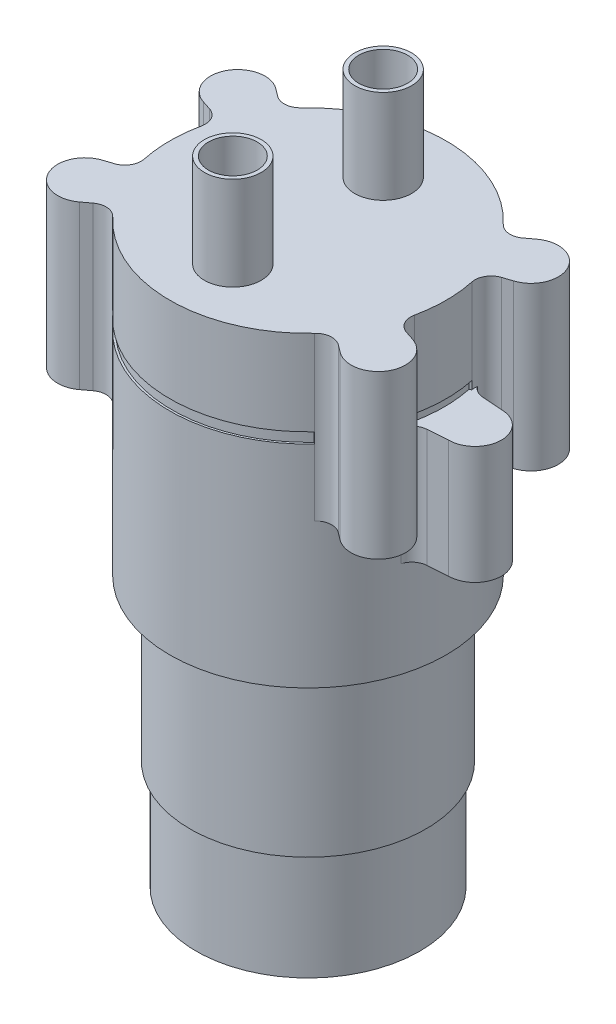
SolidWorks part; units mm, degrees
ref_plane "Plano frontal" through (0, 0, 0) normal (0, 0, 1) x (1, 0, 0)
ref_plane "Plano superior" through (0, 0, 0) normal (0, 1, 0) x (1, 0, 0)
ref_plane "Plano direito" through (0, 0, 0) normal (1, 0, 0) x (0, 0, -1)
sketch "Esboço1" plane through (0, 0, 0) normal (0, 0, 1) x (1, 0, 0)
  line L0 (0, 52.0087) -> (0, -22.4913)
  line L1 (0, 52.0087) -> (17, 52.0087)
  line L2 (17, 52.0087) -> (17, 41.5087)
  line L3 (17, 41.5087) -> (16.75, 41.5087)
  line L4 (16.75, 41.5087) -> (16.75, 40.2087)
  line L5 (16.75, 40.2087) -> (17, 40.2087)
  line L6 (17, 40.2087) -> (17, 14.2087)
  line L7 (17, 14.2087) -> (14.5, 14.2087)
  line L8 (14.5, 14.2087) -> (14.5, -5.5913)
  line L9 (14.5, -5.5913) -> (13.75, -5.5913)
  line L10 (13.75, -5.5913) -> (13.75, -18.9913)
  line L11 (13.75, -18.9913) -> (5, -18.9913)
  line L12 (5, -18.9913) -> (5, -21.4913)
  line L13 (5, -21.4913) -> (1.15, -21.4913)
  line L14 (1.15, -21.4913) -> (1.15, -22.4913)
  line L15 (1.15, -22.4913) -> (0, -22.4913)
  dimension "D1" = 1.15
  dimension "D2" = 5
  dimension "D3" = 13.75
  dimension "D4" = 14.5
  dimension "D5" = 26
  dimension "D6" = 16.75
  dimension "D7" = 1.3
  dimension "D8" = 10.5
  dimension "D9" = 19.8
  dimension "D10" = 13.4
  dimension "D11" = 2.5
  dimension "D12" = 1
revolve "Revolução1" add sketch "Esboço1" angle 360 about L0
sketch "Esboço2" plane through (0, 52.0087, 0) normal (0, 1, 0) x (1, 0, 0)
  line L0 (0, 0) -> (4.923, 2.5639) construction
  line L2 (-10.175, 0) -> (-9.846, 0) construction
  line L3 (18.0489, 9.4) -> (10.175, 0) construction
  line L4 (18.0489, -9.4) -> (10.175, 0) construction
  line L5 (18.0489, 12.75) -> (18.0489, 5.8769) construction
  line L6 (15.0926, 11.3673) -> (16.0335, 12.0759)
  line L7 (17.966, 5.8499) -> (19.0861, 6.2146)
  line L8 (15.0926, -11.3673) -> (16.0335, -12.0759)
  line L9 (17.966, -5.8499) -> (19.0861, -6.2146)
  line L10 (0, 21.7724) -> (0, 5.1279) construction
  line L11 (-18.0489, 12.75) -> (-18.0489, 5.8769) construction
  line L12 (-18.0489, -9.4) -> (-10.175, 0) construction
  line L13 (-18.0489, 9.4) -> (-10.175, 0) construction
  line L14 (0, 0) -> (-4.923, -2.5639) construction
  line L15 (0, 0) -> (-4.923, 2.5639) construction
  line L16 (-17.966, -5.8499) -> (-19.0861, -6.2146)
  line L17 (-15.0926, -11.3673) -> (-16.0335, -12.0759)
  line L18 (-17.966, 5.8499) -> (-19.0861, 6.2146)
  line L19 (-15.0926, 11.3673) -> (-16.0335, 12.0759)
  line L20 (18.0489, -5.8769) -> (18.0489, -12.75) construction
  line L21 (-18.0489, -5.8769) -> (-18.0489, -12.75) construction
  line L22 (12.4273, -11.6001) -> (0, -5.1279)
  line L23 (-12.4273, 11.6001) -> (0, 5.1279)
  line L24 (16.6289, 3.5326) -> (9.846, 0)
  line L25 (12.4273, 11.6001) -> (0, 5.1279)
  line L26 (0, -5.1279) -> (-12.4273, -11.6001)
  line L27 (0, -5.1279) -> (0, -25.7461) construction
  line L28 (-9.846, 0) -> (-16.6289, 3.5326)
  line L29 (9.846, 0) -> (10.175, 0) construction
  line L30 (-9.846, 0) -> (-16.6289, -3.5326)
  line L31 (9.846, 0) -> (16.6289, -3.5326)
  arc A0 (19.0861, 6.2146) -> (16.0335, 12.0759) centre (18.0489, 9.4) ccw
  arc A1 (16.0335, -12.0759) -> (19.0861, -6.2146) centre (18.0489, -9.4) ccw
  circle A2 centre (0, 0) radius 17 construction
  arc A4 (12.4273, 11.6001) -> (15.0926, 11.3673) centre (13.8893, 12.9648) ccw
  arc A5 (16.6289, 3.5326) -> (17.966, 5.8499) centre (18.5853, 3.9482) cw
  arc A6 (12.4273, -11.6001) -> (15.0926, -11.3673) centre (13.8893, -12.9648) cw
  arc A7 (16.6289, -3.5326) -> (17.966, -5.8499) centre (18.5853, -3.9482) ccw
  arc A11 (-16.6289, -3.5326) -> (-17.966, -5.8499) centre (-18.5853, -3.9482) cw
  arc A12 (-12.4273, -11.6001) -> (-15.0926, -11.3673) centre (-13.8893, -12.9648) ccw
  arc A13 (-16.6289, 3.5326) -> (-17.966, 5.8499) centre (-18.5853, 3.9482) ccw
  arc A14 (-12.4273, 11.6001) -> (-15.0926, 11.3673) centre (-13.8893, 12.9648) cw
  arc A15 (-16.0335, -12.0759) -> (-19.0861, -6.2146) centre (-18.0489, -9.4) cw
  arc A16 (-19.0861, 6.2146) -> (-16.0335, 12.0759) centre (-18.0489, 9.4) cw
  dimension "D1" = 6.7
  dimension "D3" = 6.7
  dimension "D4" = 2
  dimension "D2" = 25.5
extrude "Ressalto-extrusão1" add sketch "Esboço2" against normal blind 20
sketch "Esboço3" plane through (0, 52.0087, 0) normal (0, 1, 0) x (1, 0, 0)
  line L0 (23.8, 0) -> (-23.8, 0) construction
  line L1 (-20.55, -3.25) -> (-18.0656, -3.429)
  line L2 (-20.55, 3.25) -> (-18.0656, 3.429)
  line L3 (-16.2926, -4.8529) -> (-16.2926, 4.8529)
  line L4 (0, 0) -> (0, 7.288) construction
  line L5 (16.2926, -4.8529) -> (16.2926, 4.8529)
  line L6 (20.55, 3.25) -> (18.0656, 3.429)
  line L7 (20.55, -3.25) -> (18.0656, -3.429)
  arc A0 (-20.55, 3.25) -> (-20.55, -3.25) centre (-20.55, 0) ccw
  arc A1 (16.2926, 4.8529) -> (18.0656, 3.429) centre (18.2094, 5.4239) ccw
  arc A2 (-16.2926, -4.8529) -> (-18.0656, -3.429) centre (-18.2094, -5.4239) ccw
  arc A3 (-16.2926, 4.8529) -> (-18.0656, 3.429) centre (-18.2094, 5.4239) cw
  arc A4 (16.2926, -4.8529) -> (18.0656, -3.429) centre (18.2094, -5.4239) cw
  arc A5 (20.55, 3.25) -> (20.55, -3.25) centre (20.55, 0) cw
  point P11 (-16.6289, -3.5326)
  point P25 (16.6289, -3.5326)
  dimension "D2" = 6.5
  dimension "D3" = 2
  dimension "D1" = 23.8
extrude "Ressalto-extrusão2" add sketch "Esboço3" against normal blind 14.5 from offset 11.5 offset against normal yes
sketch "Esboço4" plane through (0, 52.0087, 0) normal (0, 1, 0) x (1, 0, 0)
  line L0 (0, -9.25) -> (0, 9.25)
  line L1 (0, -12.75) -> (0, 12.75) construction
  circle A0 centre (0, -9.25) radius 3.5
  circle A1 centre (0, 9.25) radius 3.5
  circle A2 centre (0, -9.25) radius 3
  circle A3 centre (0, 9.25) radius 3
  point P5 (0, 0)
  dimension "D1" = 25.5
  dimension "D2" = 7
  dimension "D3" = 6
extrude "Ressalto-extrusão3" add sketch "Esboço4" along normal blind 11.5 contours A0 L1 A2 L0 | L1 A0 L0 A2 | A3 L1 A1 L0 | L1 A3 L0 A1
